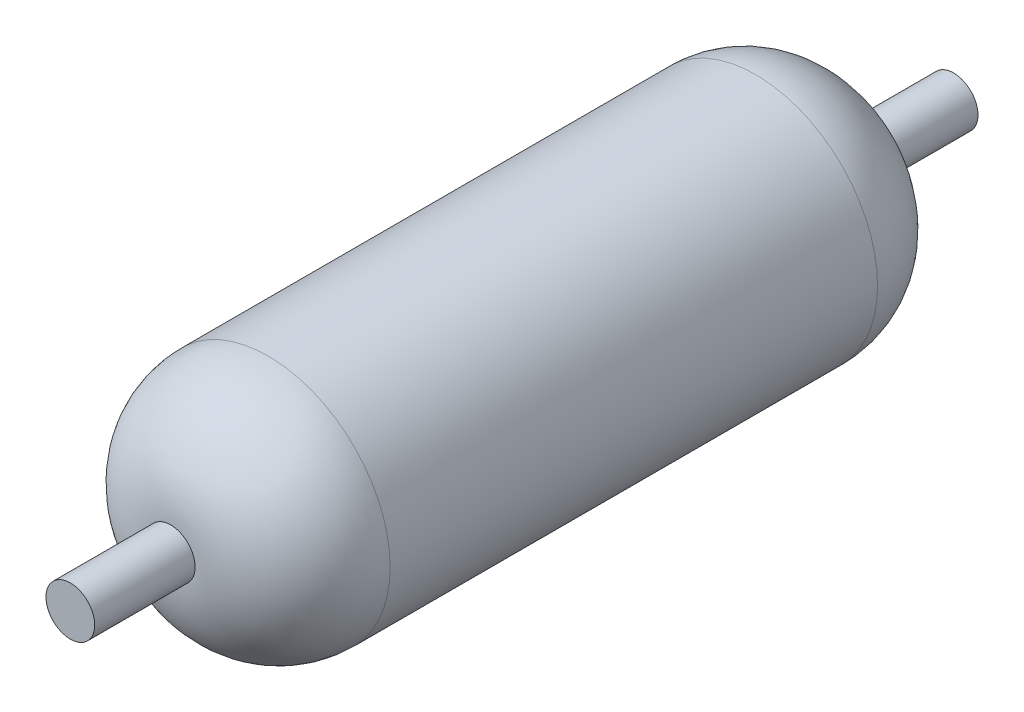
SolidWorks part; units mm, degrees
ref_plane "Front Plane" through (0, 0, 0) normal (0, 0, 1) x (1, 0, 0)
ref_plane "Top Plane" through (0, 0, 0) normal (0, 1, 0) x (1, 0, 0)
ref_plane "Right Plane" through (0, 0, 0) normal (1, 0, 0) x (0, 0, -1)
sketch "Sketch1" plane through (0, 0, 0) normal (0, 0, 1) x (1, 0, 0)
  circle A0 centre (0, 0) radius 1.25
  dimension "D1" = 2.5
extrude "Boss-Extrude1" add sketch "Sketch1" along normal mid plane 7
fillet "Fillet1" radius 1 2 edges at (1.25, 0, 3.5) (1.25, 0, -3.5)
sketch "Sketch2" plane through (0, 0, 0) normal (0, 0, 1) x (1, 0, 0)
  circle A0 centre (0, 0) radius 0.25
  dimension "D1" = 0.5
extrude "Boss-Extrude2" add sketch "Sketch2" along normal mid plane 9.06 separate body
